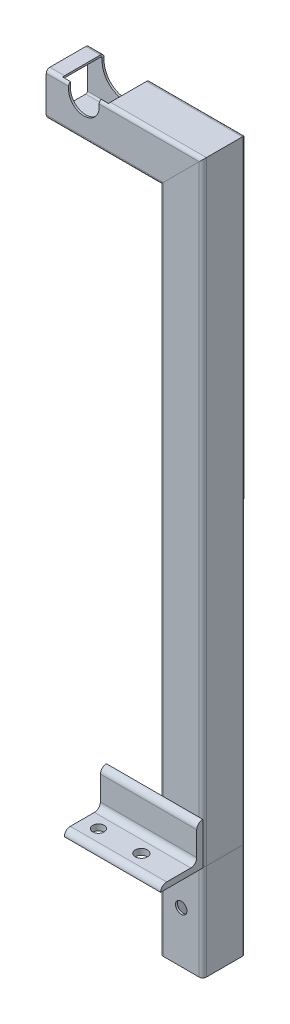
SolidWorks part; units mm, degrees
ref_plane "Front Plane" through (0, 0, 0) normal (0, 0, 1) x (1, 0, 0)
ref_plane "Top Plane" through (0, 0, 0) normal (0, 1, 0) x (1, 0, 0)
ref_plane "Right Plane" through (0, 0, 0) normal (1, 0, 0) x (0, 0, -1)
sketch "Sketch1" plane through (0, 0, 0) normal (0, 0, 1) x (1, 0, 0)
  line L0 (276.8375, 0) -> (276.8375, 491.6)
  line L1 (276.8375, 491.6) -> (164.7375, 491.6)
  line L2 (276.8375, 0) -> (276.8375, -80)
  line L3 (258.9375, 157.0549) -> (258.9375, -80) construction
  line L4 (263.7, 157.0549) -> (263.7, -80) construction
  line L5 (276.8375, 157.0549) -> (276.8375, -80) construction
  dimension "D1" = 491.6
  dimension "D2" = 80
  dimension "D3" = 112.1
  dimension "D4" = 4.7625
  dimension "D5" = 17.9
  dimension "D6" = 263.7
other "Structural MemberMain"
ref_plane "Plane1" through (276.8375, 0, 0) normal (0, 1, 0) x (-1, 0, 0)
sketch "Sketch11" plane through (276.8375, 0, 0) normal (0, 1, 0) x (-1, 0, 0)
  line L0 (-14.9, 16.3) -> (14.9, 16.3)
  line L1 (-14.9, 17.9) -> (14.9, 17.9)
  line L2 (-17.9, 14.9) -> (-17.9, -14.9)
  line L3 (-14.9, -17.9) -> (14.9, -17.9)
  line L4 (17.9, 14.9) -> (17.9, -14.9)
  line L5 (-17.9, 17.9) -> (17.9, -17.9) construction
  line L6 (-17.9, -17.9) -> (17.9, 17.9) construction
  line L7 (16.3, 14.9) -> (16.3, -14.9)
  line L8 (-14.9, -16.3) -> (14.9, -16.3)
  line L9 (-16.3, 14.9) -> (-16.3, -14.9)
  arc A0 (-17.9, -14.9) -> (-14.9, -17.9) centre (-14.9, -14.9) ccw
  arc A1 (14.9, -17.9) -> (17.9, -14.9) centre (14.9, -14.9) ccw
  arc A2 (17.9, 14.9) -> (14.9, 17.9) centre (14.9, 14.9) ccw
  arc A3 (-14.9, 17.9) -> (-17.9, 14.9) centre (-14.9, 14.9) ccw
  arc A4 (16.3, 14.9) -> (14.9, 16.3) centre (14.9, 14.9) ccw
  arc A5 (14.9, -16.3) -> (16.3, -14.9) centre (14.9, -14.9) ccw
  arc A6 (-16.3, -14.9) -> (-14.9, -16.3) centre (-14.9, -14.9) ccw
  arc A7 (-14.9, 16.3) -> (-16.3, 14.9) centre (-14.9, 14.9) ccw
  point P0 (0, 0)
  point P30 (0, 0)
  dimension "D3" = 3
  dimension "D1" = 35.8
  dimension "D2" = 35.8
  dimension "D4" = 1.6
sketch "Sketch12" plane through (0, 0, 0) normal (0, 0, 1) x (1, 0, 0)
  line L1 (196, 504.3) -> (196, 514.7) construction
  line L2 (183.3, 504.3) -> (183.3, 514.7)
  line L3 (208.7, 504.3) -> (208.7, 514.7)
  line L4 (276.8375, 491.6) -> (164.7375, 491.6) construction
  line L5 (164.7375, 509.5) -> (294.7375, 509.5) construction
  arc A0 (183.3, 504.3) -> (208.7, 504.3) centre (196, 504.3) ccw
  arc A1 (208.7, 514.7) -> (183.3, 514.7) centre (196, 514.7) ccw
  point P2 (196, 509.5)
  dimension "D1" = 25.4
  dimension "D2" = 196
extrude "Cut-ExtrudeTopRailGuide" cut sketch "Sketch12" against normal through all and the other way through all
sketch "Sketch13" plane through (0, 0, 0) normal (0, 1, 0) x (1, 0, 0)
  line L0 (214.7375, -17.9) -> (294.7375, -17.9)
  line L1 (208.7, -17.9) -> (291.7375, -17.9) construction
  line L3 (294.7375, 14.9) -> (294.7375, -14.9) construction
  point P4 (254.7375, -17.9)
  dimension "D1" = 80
other "Structural MemberAngle"
ref_plane "Plane2" through (214.7375, 0, 17.9) normal (1, 0, 0) x (0, 1, 0)
sketch "Sketch14" plane through (214.7375, 0, 17.9) normal (1, 0, 0) x (0, 1, 0)
  line L0 (0, 0) -> (0, 35)
  line L1 (0, 17.5) -> (5, 17.5) construction
  line L2 (5, 30) -> (5, 10)
  line L3 (10, 5) -> (30, 5)
  line L4 (17.5, 5) -> (17.5, 0) construction
  line L5 (35, 0) -> (0, 0)
  arc A0 (35, 0) -> (30, 5) centre (30, 0) ccw
  arc A1 (0, 35) -> (5, 30) centre (0, 30) cw
  arc A2 (10, 5) -> (5, 10) centre (10, 10) cw
  point P10 (17.5, 0)
  point P14 (0, 17.5)
  point P15 (5, 17.5)
  point P16 (17.5, 5)
  point P17 (5, 35)
  point P18 (35, 5)
  point P21 (0, 0)
  dimension "D2" = 5
  dimension "D3" = 35
  dimension "Radius_1" = 5
  dimension "D1" = 5
sketch "Sketch15" plane through (0, 0, 0) normal (0, 1, 0) x (1, 0, 0)
  line L0 (254.7375, -17.9) -> (254.7375, -52.9) construction
  line L1 (294.7375, -52.9) -> (214.7375, -52.9) construction
  line L2 (-65.8005, -37.9) -> (575.2755, -37.9) construction
  line L3 (214.7375, -17.9) -> (294.7375, -17.9) construction
  line L4 (0, 28.933) -> (0, -28.933) construction
  circle A0 centre (228.1, -37.9) radius 4.7625
  circle A1 centre (263.7, -37.9) radius 5.0441
  point P7 (254.7375, -37.9)
  point P16 (0, 0)
  dimension "D2" = 9.525
  dimension "D1" = 20
  dimension "D3" = 263.7
  dimension "D4" = 35.6
extrude "Cut-ExtrudeMountingHoles" cut sketch "Sketch15" along normal through all
sketch "Sketch16" plane through (0, 0, 0) normal (0, 0, 1) x (1, 0, 0)
  line L4 (215.05, 504.3) -> (215.05, 514.7)
  line L5 (176.95, 514.7) -> (176.95, 504.3)
  line L6 (215.05, 504.3) -> (215.05, 514.7)
  line L7 (176.95, 514.7) -> (176.95, 504.3)
  arc A4 (176.95, 504.3) -> (215.05, 504.3) centre (196, 504.3) ccw
  arc A5 (215.05, 514.7) -> (176.95, 514.7) centre (196, 514.7) ccw
  arc A6 (176.95, 504.3) -> (215.05, 504.3) centre (196, 504.3) ccw
  arc A7 (215.05, 514.7) -> (176.95, 514.7) centre (196, 514.7) ccw
  dimension "D1" = 6.35
extrude "Cut-ExtrudeEnlargeRailGuide" cut sketch "Sketch16" against normal through all and the other way up to surface other way up to face at (208.3938, 496.9125, 16.3)
sketch "Sketch17" plane through (0, 0, 17.9) normal (0, 0, 1) x (1, 0, 0)
  line L0 (276.8375, 0) -> (276.8375, -80) construction
  line L1 (214.7375, 0) -> (294.7375, 0) construction
  line L2 (294.7375, 0) -> (294.7375, -80) construction
  circle A0 centre (276.8375, -37.5) radius 4.7625
  dimension "D1" = 9.525
  dimension "D2" = 37.5
  dimension "D3" = 17.9
extrude "Cut-Extrude1" cut sketch "Sketch17" against normal through all
